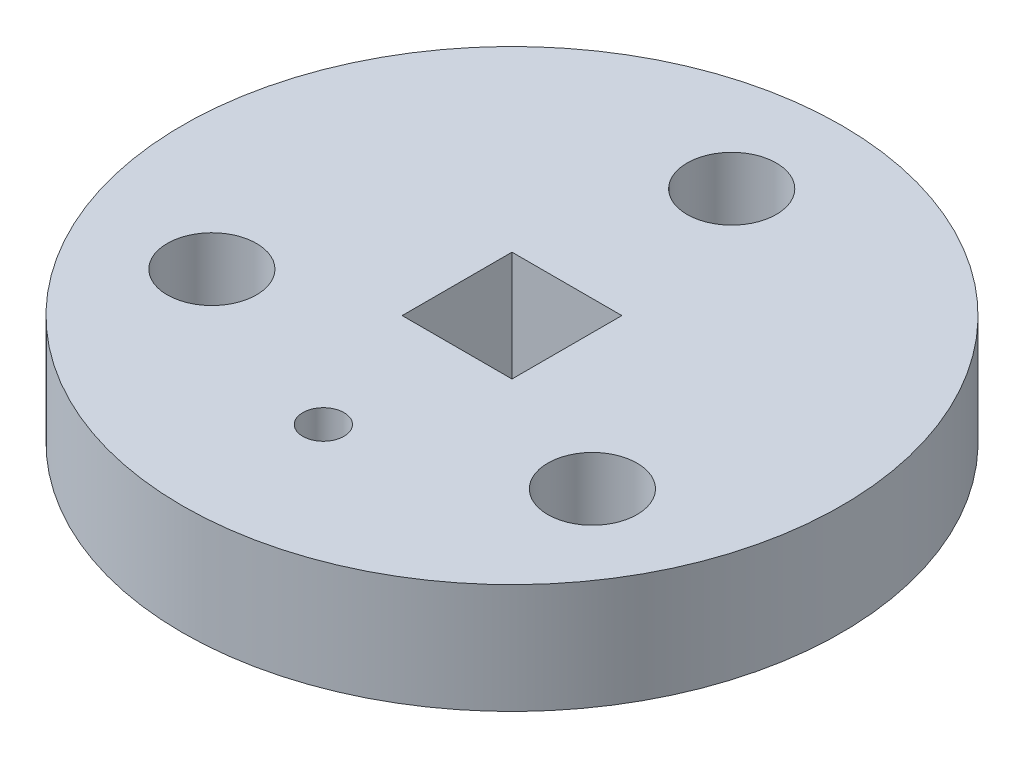
SolidWorks part; units mm, degrees
ref_plane "Front Plane" through (0, 0, 0) normal (0, 0, 1) x (1, 0, 0)
ref_plane "Top Plane" through (0, 0, 0) normal (0, 1, 0) x (1, 0, 0)
ref_plane "Right Plane" through (0, 0, 0) normal (1, 0, 0) x (0, 0, -1)
sketch "Sketch1" plane through (0, 0, 0) normal (0, 1, 0) x (1, 0, 0)
  line L0 (0, -2.794) -> (0, -19.0128) construction
  line L1 (3.175, -3.175) -> (-3.175, -3.175)
  line L2 (3.175, -3.175) -> (3.175, 3.175)
  line L3 (3.175, 3.175) -> (-3.175, 3.175)
  line L4 (-3.175, -3.175) -> (-3.175, 3.175)
  line L7 (0, 0) -> (0, 12.7) construction
  line L8 (0, 0) -> (10.9985, -6.35) construction
  line L9 (0, 0) -> (-10.9985, -6.35) construction
  circle A0 centre (0, 0) radius 19.05
  arc A1 (1.1906, -10.9034) -> (-1.1906, -10.9034) centre (0, -10.9034) ccw
  circle A4 centre (0, 12.7) radius 2.5797
  circle A5 centre (10.9985, -6.35) radius 2.5797
  circle A6 centre (-10.9985, -6.35) radius 2.5797
  arc A7 (-1.1906, -10.9034) -> (1.1906, -10.9034) centre (0, -10.9034) ccw
  point P7 (0, -3.175)
  point P8 (-3.175, 0)
  point P15 (0, 0)
  point P23 (-1.1906, -19.0128)
  point P28 (0, 0)
  dimension "D1" = 38.1
  dimension "D3" = 2.3813
  dimension "D7" = 5.1594
  dimension "D2" = 6.35
  dimension "D5" = 2.794
  dimension "D6" = 12.7
  dimension "D8" = 3
extrude "Boss-Extrude1" add sketch "Sketch1" along normal blind 6.35
